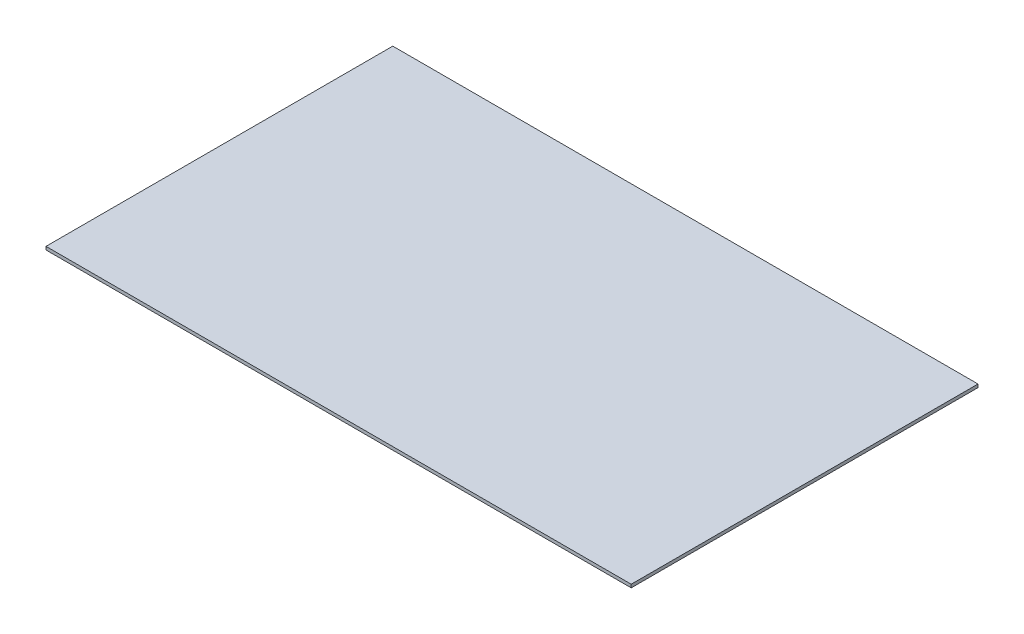
SolidWorks part; units mm, degrees
ref_plane "Front Plane" through (0, 0, 0) normal (0, 0, 1) x (1, 0, 0)
ref_plane "Top Plane" through (0, 0, 0) normal (0, 1, 0) x (1, 0, 0)
ref_plane "Right Plane" through (0, 0, 0) normal (1, 0, 0) x (0, 0, -1)
sketch "Sketch1" plane through (0, 0, 0) normal (0, 1, 0) x (1, 0, 0)
  line L1 (0, 0) -> (514.35, 0)
  line L2 (0, 0) -> (0, 304.8)
  line L3 (0, 304.8) -> (514.35, 304.8)
  line L4 (514.35, 0) -> (514.35, 304.8)
  dimension "D1" = 514.35
  dimension "D2" = 304.8
extrude "Boss-Extrude1" add sketch "Sketch1" along normal blind 2.794
sketch "Sketch3" plane through (0, 2.794, 0) normal (0, 1, 0) x (1, 0, 0)
  line L0 (152.4, 342.4398) -> (152.4, -37.6398) construction
  line L1 (0, 304.8) -> (0, 0) construction
  line L2 (20.4177, 228.6) -> (20.4177, 76.2) construction
  line L4 (514.35, 304.8) -> (0, 304.8) construction
  line L5 (152.4, 304.8) -> (76.2, 284.3823) construction
  line L6 (76.2, 284.3823) -> (20.4177, 228.6) construction
  line L7 (20.4177, 228.6) -> (0, 152.4) construction
  line L8 (0, 152.4) -> (20.4177, 76.2) construction
  line L9 (20.4177, 76.2) -> (76.2, 20.4177) construction
  line L10 (76.2, 20.4177) -> (152.4, 0) construction
  line L11 (152.4, 0) -> (228.6, 20.4177) construction
  line L12 (228.6, 20.4177) -> (284.3823, 76.2) construction
  line L13 (284.3823, 76.2) -> (304.8, 152.4) construction
  line L14 (304.8, 152.4) -> (284.3823, 228.6) construction
  line L15 (284.3823, 228.6) -> (228.6, 284.3823) construction
  line L16 (228.6, 284.3823) -> (152.4, 304.8) construction
  circle A0 centre (152.4, 152.4) radius 147.2071 construction
  dimension "D1" = 152.4
  dimension "D3" = 304.8
